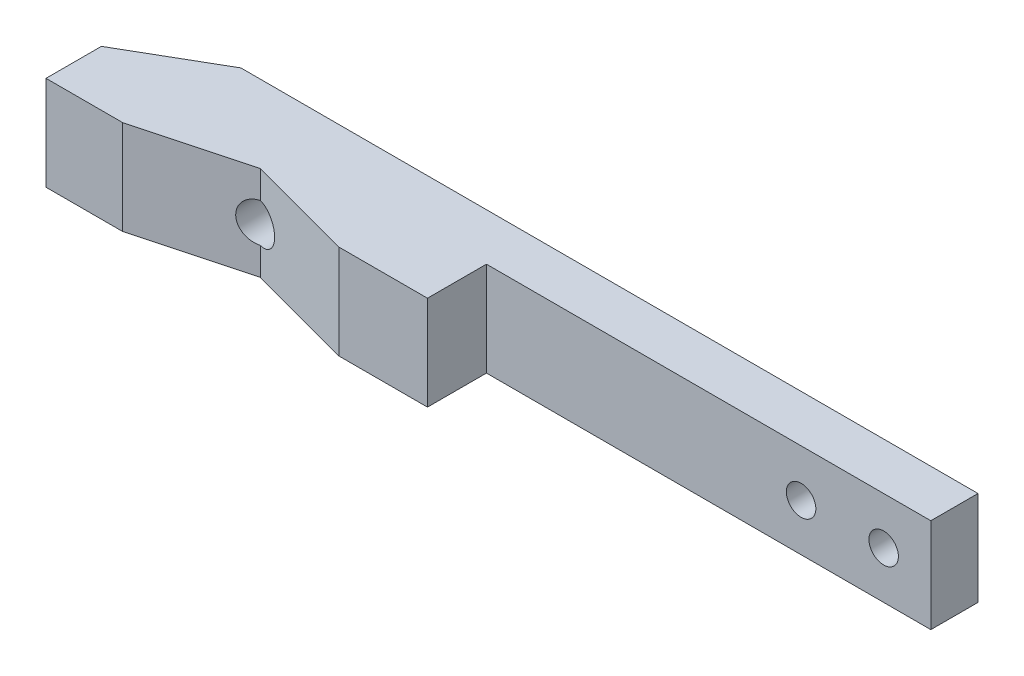
SolidWorks part; units mm, degrees
material "POM Acetal Copolymer"
ref_plane "Front Plane" through (0, 0, 0) normal (0, 0, 1) x (1, 0, 0)
ref_plane "Top Plane" through (0, 0, 0) normal (0, 1, 0) x (1, 0, 0)
ref_plane "Right Plane" through (0, 0, 0) normal (1, 0, 0) x (0, 0, -1)
sketch "Sketch1" plane through (0, 0, 0) normal (0, 1, 0) x (1, 0, 0)
  line L4 (35.397, 0.2122) -> (35.397, -3.7878)
  line L5 (-34.6011, 3.7026) -> (35.397, -3.7878) construction
  line L6 (-34.6029, -4.1177) -> (35.397, 4.2122) construction
  line L8 (-34.6029, -4.1177) -> (-34.6029, -8.8148)
  line L9 (-34.6029, -8.8148) -> (-28.1029, -8.8148)
  line L13 (-2.2832, -3.7878) -> (35.397, -3.7878)
  line L18 (-9.7832, -8.7878) -> (-2.2832, -8.7878)
  line L19 (-2.2832, -8.7878) -> (-2.2832, -3.7878)
  line L22 (-28.1029, -8.8148) -> (-18.8926, -6.3469)
  line L23 (-9.7832, -8.7878) -> (-18.8926, -6.3469)
  line L24 (35.397, 0.2122) -> (-27.1033, 0.2122)
  line L25 (-34.6029, -4.1177) -> (-27.1033, 0.2122)
  point P0 (0, 0)
  dimension "D1" = 8
  dimension "D2" = 70
  dimension "D3" = 7.5
  dimension "D4" = 18.3197
  dimension "D5" = 6.5
  dimension "D6" = 15
  dimension "D7" = 15
  dimension "D8" = 37.6803
  dimension "D9" = 60
extrude "Boss-Extrude2" add sketch "Sketch1" along normal blind 8
hole_wizard "M3 Tapped Hole1" positions "Sketch2" profile "Sketch3" tap size "M3" standard "DIN"
sketch "Sketch2" plane through (0, 0, -0.2122) normal (0, 0, -1) x (-1, 0, 0)
  line L0 (-35.397, 8) -> (-35.397, 0) construction
  point P0 (-31.397, 4)
  point P2 (-24.397, 4)
  dimension "D1" = 4
  dimension "D2" = 7
sketch "Sketch3" plane through (31.397, 4, -0.2122) normal (1, 0, 0) x (0, 1, 0)
  line L0 (0, 0) -> (0, 9.2511)
  line L1 (0, 9.2511) -> (1.25, 8.5)
  line L2 (1.25, 8.5) -> (1.25, 0)
  line L5 (1.25, 0) -> (0, 0)
  line L10 (0, 9.2511) -> (-1.25, 8.5) construction
  line L11 (0, -6.35) -> (0, 107.95) construction
  dimension "Tap Drill Dia." = 2.5
  dimension "Tap Drill Depth" = 8.5
  dimension "Drill Angle" = 118
cosmetic thread "Hole Thread1"
cosmetic thread "Hole Thread2"
hole_wizard "M4 Tapped Hole1" positions "Sketch4" profile "Sketch5" tap size "M4" standard "DIN"
sketch "Sketch4" plane through (0, 0, -0.2122) normal (0, 0, -1) x (-1, 0, 0)
  line L1 (34.6029, 8) -> (34.6029, 0) construction
  point P0 (18.8929, 4)
  dimension "D1" = 15.71
sketch "Sketch5" plane through (-18.8929, 4, -0.2122) normal (1, 0, 0) x (0, 1, 0)
  line L0 (0, 0) -> (0, 12.4914)
  line L1 (0, 12.4914) -> (1.65, 11.5)
  line L2 (1.65, 11.5) -> (1.65, 0)
  line L5 (1.65, 0) -> (0, 0)
  line L10 (0, 12.4914) -> (-1.65, 11.5) construction
  line L11 (0, -6.35) -> (0, 107.95) construction
  dimension "Tap Drill Dia." = 3.3
  dimension "Tap Drill Depth" = 11.5
  dimension "Drill Angle" = 118
cosmetic thread "Hole Thread3"
